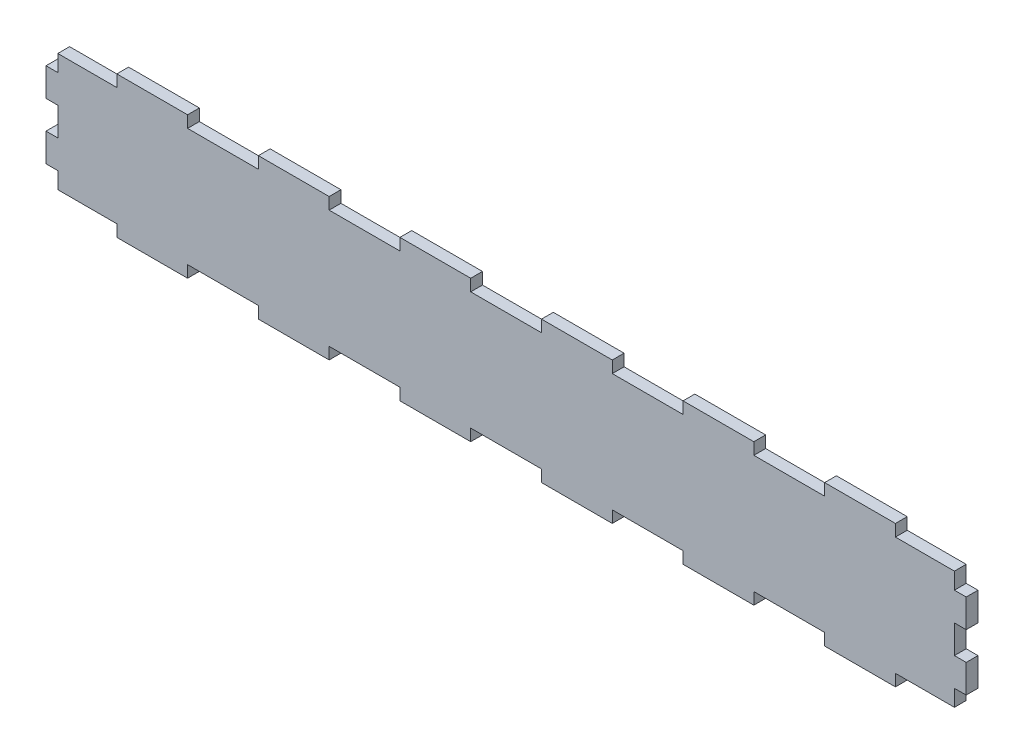
SolidWorks part; units mm, degrees
ref_plane "Plan de face" through (0, 0, 0) normal (0, 0, 1) x (1, 0, 0)
ref_plane "Plan de dessus" through (0, 0, 0) normal (0, 1, 0) x (1, 0, 0)
ref_plane "Plan de droite" through (0, 0, 0) normal (1, 0, 0) x (0, 0, -1)
sketch "Esquisse1" plane through (0, 0, 0) normal (0, 0, 1) x (1, 0, 0)
  line L1 (0, 0) -> (390, 0)
  line L2 (0, 0) -> (0, -60)
  line L3 (0, -60) -> (390, -60)
  line L4 (390, 0) -> (390, -60)
  dimension "D1" = 390
  dimension "D2" = 60
extrude "Boss.-Extru.1" add sketch "Esquisse1" along normal blind 5
sketch "Esquisse2" plane through (0, 0, 5) normal (0, 0, 1) x (1, 0, 0)
  line L0 (0, 0) -> (390, 0) construction
  line L1 (0, -60) -> (30, -60)
  line L2 (0, -60) -> (0, -55)
  line L3 (0, -55) -> (30, -55)
  line L4 (30, -60) -> (30, -55)
  dimension "D1" = 390
  dimension "D2" = 30
  dimension "D3" = 5
extrude "Enlèv. mat.-Extru.1" cut sketch "Esquisse2" against normal blind 5
pattern_linear "Répétition linéaire1" count 7 spacing 60 along (1, 0, 0) of "Enlèv. mat.-Extru.1"
sketch "Esquisse3" plane through (0, 0, 5) normal (0, 0, 1) x (1, 0, 0)
  line L0 (30, -60) -> (60, -60) construction
  line L1 (0, -60) -> (5, -60)
  line L2 (0, -60) -> (0, -48)
  line L3 (0, -48) -> (5, -48)
  line L4 (5, -60) -> (5, -48)
  line L5 (0, 0) -> (0, -55) construction
  line L6 (42.6379, -60) -> (42.6379, 0) construction
  line L7 (390, 0) -> (0, 0) construction
  dimension "D2" = 60
  dimension "D1" = 5
  dimension "D3" = 12
extrude "Enlèv. mat.-Extru.2" cut sketch "Esquisse3" against normal blind 5
pattern_linear "Répétition linéaire2" count 3 spacing 24 along (0, 1, 0) of "Enlèv. mat.-Extru.2"
ref_plane "Plan1" through (195, 0, 0) normal (-1, 0, 0) x (0, 0, 1)
mirror "Symétrie1" about plane through (195, 0, 0) normal (-1, 0, 0) of "Répétition linéaire2", "Enlèv. mat.-Extru.2"
ref_plane "Plan2" through (0, -30, 0) normal (0, -1, 0) x (-1, 0, 0)
mirror "Symétrie2" about plane through (0, -30, 0) normal (0, -1, 0) of "Répétition linéaire1", "Enlèv. mat.-Extru.1"
equation "\"D1@Esquisse1\"=400-10"
equation "\"D2@Esquisse2\"=\"D1@Esquisse2\"/13"
equation "\"D3@Esquisse3\"=\"D2@Esquisse3\"/5"
